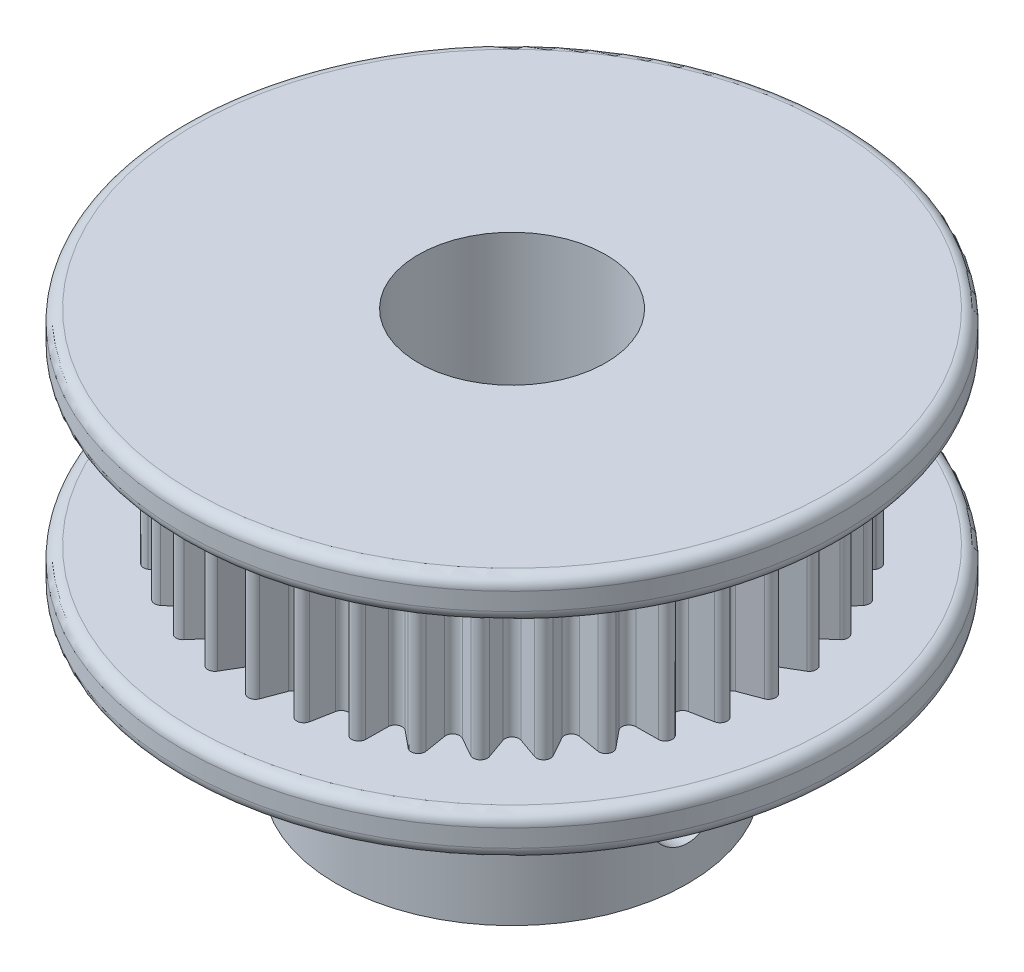
SolidWorks part; units mm, degrees
material "6063-T5"
ref_plane "Front Plane" through (0, 0, 0) normal (0, 0, 1) x (1, 0, 0)
ref_plane "Top Plane" through (0, 0, 0) normal (0, 1, 0) x (1, 0, 0)
ref_plane "Right Plane" through (0, 0, 0) normal (1, 0, 0) x (0, 0, -1)
sketch "Sketch1" plane through (0, 0, 0) normal (0, 1, 0) x (1, 0, 0)
  circle A0 centre (0, 0) radius 7.5
  dimension "D1" = 15
extrude "Boss-Extrude1" add sketch "Sketch1" along normal blind 7 contours A0
sketch "Sketch7" plane through (0, 7, 0) normal (0, 1, 0) x (1, 0, 0)
  circle A0 centre (0, 0) radius 14.065
  dimension "D1" = 28.13
extrude "Boss-Extrude5" add sketch "Sketch7" along normal blind 1.75
sketch "Sketch9" plane through (0, 8.75, 0) normal (0, 1, 0) x (1, 0, 0)
  line L0 (0.2807, 11.056) -> (0.6178, 10.1631)
  line L1 (1.1564, 10.116) -> (1.6435, 10.9367)
  line L2 (0, 10.95) -> (0, 0) construction
  line L3 (1.9014, 10.7836) -> (0, 0) construction
  line L4 (2.1962, 10.8393) -> (2.3732, 9.9015)
  line L5 (0, 10.95) -> (1.9014, 10.7836) construction
  line L6 (0.9507, 10.8668) -> (0, 0)
  line L7 (2.8955, 9.7615) -> (3.5176, 10.4852)
  line L8 (4.0451, 10.2932) -> (4.0565, 9.3389)
  line L9 (4.5466, 9.1104) -> (5.2849, 9.7151)
  line L10 (5.771, 9.4344) -> (5.6166, 8.4926)
  line L11 (6.0595, 8.1825) -> (6.8916, 8.6498)
  line L12 (7.3216, 8.289) -> (7.006, 7.3883)
  line L13 (7.3883, 7.006) -> (8.289, 7.3216)
  line L14 (8.6498, 6.8916) -> (8.1825, 6.0595)
  line L15 (8.4926, 5.6166) -> (9.4344, 5.771)
  line L16 (9.7151, 5.2849) -> (9.1104, 4.5466)
  line L17 (9.3389, 4.0565) -> (10.2932, 4.0451)
  line L18 (10.4852, 3.5176) -> (9.7615, 2.8955)
  line L19 (9.9015, 2.3732) -> (10.8393, 2.1962)
  line L20 (10.9367, 1.6435) -> (10.116, 1.1564)
  line L21 (10.1631, 0.6178) -> (11.056, 0.2807)
  line L22 (11.056, -0.2807) -> (10.1631, -0.6178)
  line L23 (10.116, -1.1564) -> (10.9367, -1.6435)
  line L24 (10.8393, -2.1962) -> (9.9015, -2.3732)
  line L25 (9.7615, -2.8955) -> (10.4852, -3.5176)
  line L26 (10.2932, -4.0451) -> (9.3389, -4.0565)
  line L27 (9.1104, -4.5466) -> (9.7151, -5.2849)
  line L28 (9.4344, -5.771) -> (8.4926, -5.6166)
  line L29 (8.1825, -6.0595) -> (8.6498, -6.8916)
  line L30 (8.289, -7.3216) -> (7.3883, -7.006)
  line L31 (7.006, -7.3883) -> (7.3216, -8.289)
  line L32 (6.8916, -8.6498) -> (6.0595, -8.1825)
  line L33 (5.6166, -8.4926) -> (5.771, -9.4344)
  line L34 (5.2849, -9.7151) -> (4.5466, -9.1104)
  line L35 (4.0565, -9.3389) -> (4.0451, -10.2932)
  line L36 (3.5176, -10.4852) -> (2.8955, -9.7615)
  line L37 (2.3732, -9.9015) -> (2.1962, -10.8393)
  line L38 (1.6435, -10.9367) -> (1.1564, -10.116)
  line L39 (0.6178, -10.1631) -> (0.2807, -11.056)
  line L40 (-0.2807, -11.056) -> (-0.6178, -10.1631)
  line L41 (-1.1564, -10.116) -> (-1.6435, -10.9367)
  line L42 (-2.1962, -10.8393) -> (-2.3732, -9.9015)
  line L43 (-2.8955, -9.7615) -> (-3.5176, -10.4852)
  line L44 (-4.0451, -10.2932) -> (-4.0565, -9.3389)
  line L45 (-4.5466, -9.1104) -> (-5.2849, -9.7151)
  line L46 (-5.771, -9.4344) -> (-5.6166, -8.4926)
  line L47 (-6.0595, -8.1825) -> (-6.8916, -8.6498)
  line L48 (-7.3216, -8.289) -> (-7.006, -7.3883)
  line L49 (-7.3883, -7.006) -> (-8.289, -7.3216)
  line L50 (-8.6498, -6.8916) -> (-8.1825, -6.0595)
  line L51 (-8.4926, -5.6166) -> (-9.4344, -5.771)
  line L52 (-9.7151, -5.2849) -> (-9.1104, -4.5466)
  line L53 (-9.3389, -4.0565) -> (-10.2932, -4.0451)
  line L54 (-10.4852, -3.5176) -> (-9.7615, -2.8955)
  line L55 (-9.9015, -2.3732) -> (-10.8393, -2.1962)
  line L56 (-10.9367, -1.6435) -> (-10.116, -1.1564)
  line L57 (-10.1631, -0.6178) -> (-11.056, -0.2807)
  line L58 (-11.056, 0.2807) -> (-10.1631, 0.6178)
  line L59 (-10.116, 1.1564) -> (-10.9367, 1.6435)
  line L60 (-10.8393, 2.1962) -> (-9.9015, 2.3732)
  line L61 (-9.7615, 2.8955) -> (-10.4852, 3.5176)
  line L62 (-10.2932, 4.0451) -> (-9.3389, 4.0565)
  line L63 (-9.1104, 4.5466) -> (-9.7151, 5.2849)
  line L64 (-9.4344, 5.771) -> (-8.4926, 5.6166)
  line L65 (-8.1825, 6.0595) -> (-8.6498, 6.8916)
  line L66 (-8.289, 7.3216) -> (-7.3883, 7.006)
  line L67 (-7.006, 7.3883) -> (-7.3216, 8.289)
  line L68 (-6.8916, 8.6498) -> (-6.0595, 8.1825)
  line L69 (-5.6166, 8.4926) -> (-5.771, 9.4344)
  line L70 (-5.2849, 9.7151) -> (-4.5466, 9.1104)
  line L71 (-4.0565, 9.3389) -> (-4.0451, 10.2932)
  line L72 (-3.5176, 10.4852) -> (-2.8955, 9.7615)
  line L73 (-2.3732, 9.9015) -> (-2.1962, 10.8393)
  line L74 (-1.6435, 10.9367) -> (-1.1564, 10.116)
  line L75 (-0.6178, 10.1631) -> (-0.2807, 11.056)
  circle A0 centre (0, 0) radius 11.25 construction
  arc A1 (0.2807, 11.056) -> (0, 11.25) centre (0, 10.95) ccw
  arc A2 (2.1962, 10.8393) -> (1.9535, 11.0791) centre (1.9014, 10.7836) ccw
  arc A3 (1.9535, 11.0791) -> (1.6435, 10.9367) centre (1.9014, 10.7836) ccw
  arc A4 (0.6178, 10.1631) -> (1.1564, 10.116) centre (0.8984, 10.2691) ccw
  arc A5 (2.3732, 9.9015) -> (2.8955, 9.7615) centre (2.668, 9.9571) ccw
  arc A6 (3.8477, 10.5715) -> (3.5176, 10.4852) centre (3.7451, 10.2896) ccw
  arc A7 (4.0451, 10.2932) -> (3.8477, 10.5715) centre (3.7451, 10.2896) ccw
  arc A8 (4.0565, 9.3389) -> (4.5466, 9.1104) centre (4.3565, 9.3425) ccw
  arc A9 (5.625, 9.7428) -> (5.2849, 9.7151) centre (5.475, 9.483) ccw
  arc A10 (5.771, 9.4344) -> (5.625, 9.7428) centre (5.475, 9.483) ccw
  arc A11 (5.6166, 8.4926) -> (6.0595, 8.1825) centre (5.9126, 8.4441) ccw
  arc A12 (7.2314, 8.618) -> (6.8916, 8.6498) centre (7.0385, 8.3882) ccw
  arc A13 (7.3216, 8.289) -> (7.2314, 8.618) centre (7.0385, 8.3882) ccw
  arc A14 (7.006, 7.3883) -> (7.3883, 7.006) centre (7.2891, 7.2891) ccw
  arc A15 (8.618, 7.2314) -> (8.289, 7.3216) centre (8.3882, 7.0385) ccw
  arc A16 (8.6498, 6.8916) -> (8.618, 7.2314) centre (8.3882, 7.0385) ccw
  arc A17 (8.1825, 6.0595) -> (8.4926, 5.6166) centre (8.4441, 5.9126) ccw
  arc A18 (9.7428, 5.625) -> (9.4344, 5.771) centre (9.483, 5.475) ccw
  arc A19 (9.7151, 5.2849) -> (9.7428, 5.625) centre (9.483, 5.475) ccw
  arc A20 (9.1104, 4.5466) -> (9.3389, 4.0565) centre (9.3425, 4.3565) ccw
  arc A21 (10.5715, 3.8477) -> (10.2932, 4.0451) centre (10.2896, 3.7451) ccw
  arc A22 (10.4852, 3.5176) -> (10.5715, 3.8477) centre (10.2896, 3.7451) ccw
  arc A23 (9.7615, 2.8955) -> (9.9015, 2.3732) centre (9.9571, 2.668) ccw
  arc A24 (11.0791, 1.9535) -> (10.8393, 2.1962) centre (10.7836, 1.9014) ccw
  arc A25 (10.9367, 1.6435) -> (11.0791, 1.9535) centre (10.7836, 1.9014) ccw
  arc A26 (10.116, 1.1564) -> (10.1631, 0.6178) centre (10.2691, 0.8984) ccw
  arc A27 (11.25, 0) -> (11.056, 0.2807) centre (10.95, 0) ccw
  arc A28 (11.056, -0.2807) -> (11.25, 0) centre (10.95, 0) ccw
  arc A29 (10.1631, -0.6178) -> (10.116, -1.1564) centre (10.2691, -0.8984) ccw
  arc A30 (11.0791, -1.9535) -> (10.9367, -1.6435) centre (10.7836, -1.9014) ccw
  arc A31 (10.8393, -2.1962) -> (11.0791, -1.9535) centre (10.7836, -1.9014) ccw
  arc A32 (9.9015, -2.3732) -> (9.7615, -2.8955) centre (9.9571, -2.668) ccw
  arc A33 (10.5715, -3.8477) -> (10.4852, -3.5176) centre (10.2896, -3.7451) ccw
  arc A34 (10.2932, -4.0451) -> (10.5715, -3.8477) centre (10.2896, -3.7451) ccw
  arc A35 (9.3389, -4.0565) -> (9.1104, -4.5466) centre (9.3425, -4.3565) ccw
  arc A36 (9.7428, -5.625) -> (9.7151, -5.2849) centre (9.483, -5.475) ccw
  arc A37 (9.4344, -5.771) -> (9.7428, -5.625) centre (9.483, -5.475) ccw
  arc A38 (8.4926, -5.6166) -> (8.1825, -6.0595) centre (8.4441, -5.9126) ccw
  arc A39 (8.618, -7.2314) -> (8.6498, -6.8916) centre (8.3882, -7.0385) ccw
  arc A40 (8.289, -7.3216) -> (8.618, -7.2314) centre (8.3882, -7.0385) ccw
  arc A41 (7.3883, -7.006) -> (7.006, -7.3883) centre (7.2891, -7.2891) ccw
  arc A42 (7.2314, -8.618) -> (7.3216, -8.289) centre (7.0385, -8.3882) ccw
  arc A43 (6.8916, -8.6498) -> (7.2314, -8.618) centre (7.0385, -8.3882) ccw
  arc A44 (6.0595, -8.1825) -> (5.6166, -8.4926) centre (5.9126, -8.4441) ccw
  arc A45 (5.625, -9.7428) -> (5.771, -9.4344) centre (5.475, -9.483) ccw
  arc A46 (5.2849, -9.7151) -> (5.625, -9.7428) centre (5.475, -9.483) ccw
  arc A47 (4.5466, -9.1104) -> (4.0565, -9.3389) centre (4.3565, -9.3425) ccw
  arc A48 (3.8477, -10.5715) -> (4.0451, -10.2932) centre (3.7451, -10.2896) ccw
  arc A49 (3.5176, -10.4852) -> (3.8477, -10.5715) centre (3.7451, -10.2896) ccw
  arc A50 (2.8955, -9.7615) -> (2.3732, -9.9015) centre (2.668, -9.9571) ccw
  arc A51 (1.9535, -11.0791) -> (2.1962, -10.8393) centre (1.9014, -10.7836) ccw
  arc A52 (1.6435, -10.9367) -> (1.9535, -11.0791) centre (1.9014, -10.7836) ccw
  arc A53 (1.1564, -10.116) -> (0.6178, -10.1631) centre (0.8984, -10.2691) ccw
  arc A54 (0, -11.25) -> (0.2807, -11.056) centre (0, -10.95) ccw
  arc A55 (-0.2807, -11.056) -> (0, -11.25) centre (0, -10.95) ccw
  arc A56 (-0.6178, -10.1631) -> (-1.1564, -10.116) centre (-0.8984, -10.2691) ccw
  arc A57 (-1.9535, -11.0791) -> (-1.6435, -10.9367) centre (-1.9014, -10.7836) ccw
  arc A58 (-2.1962, -10.8393) -> (-1.9535, -11.0791) centre (-1.9014, -10.7836) ccw
  arc A59 (-2.3732, -9.9015) -> (-2.8955, -9.7615) centre (-2.668, -9.9571) ccw
  arc A60 (-3.8477, -10.5715) -> (-3.5176, -10.4852) centre (-3.7451, -10.2896) ccw
  arc A61 (-4.0451, -10.2932) -> (-3.8477, -10.5715) centre (-3.7451, -10.2896) ccw
  arc A62 (-4.0565, -9.3389) -> (-4.5466, -9.1104) centre (-4.3565, -9.3425) ccw
  arc A63 (-5.625, -9.7428) -> (-5.2849, -9.7151) centre (-5.475, -9.483) ccw
  arc A64 (-5.771, -9.4344) -> (-5.625, -9.7428) centre (-5.475, -9.483) ccw
  arc A65 (-5.6166, -8.4926) -> (-6.0595, -8.1825) centre (-5.9126, -8.4441) ccw
  arc A66 (-7.2314, -8.618) -> (-6.8916, -8.6498) centre (-7.0385, -8.3882) ccw
  arc A67 (-7.3216, -8.289) -> (-7.2314, -8.618) centre (-7.0385, -8.3882) ccw
  arc A68 (-7.006, -7.3883) -> (-7.3883, -7.006) centre (-7.2891, -7.2891) ccw
  arc A69 (-8.618, -7.2314) -> (-8.289, -7.3216) centre (-8.3882, -7.0385) ccw
  arc A70 (-8.6498, -6.8916) -> (-8.618, -7.2314) centre (-8.3882, -7.0385) ccw
  arc A71 (-8.1825, -6.0595) -> (-8.4926, -5.6166) centre (-8.4441, -5.9126) ccw
  arc A72 (-9.7428, -5.625) -> (-9.4344, -5.771) centre (-9.483, -5.475) ccw
  arc A73 (-9.7151, -5.2849) -> (-9.7428, -5.625) centre (-9.483, -5.475) ccw
  arc A74 (-9.1104, -4.5466) -> (-9.3389, -4.0565) centre (-9.3425, -4.3565) ccw
  arc A75 (-10.5715, -3.8477) -> (-10.2932, -4.0451) centre (-10.2896, -3.7451) ccw
  arc A76 (-10.4852, -3.5176) -> (-10.5715, -3.8477) centre (-10.2896, -3.7451) ccw
  arc A77 (-9.7615, -2.8955) -> (-9.9015, -2.3732) centre (-9.9571, -2.668) ccw
  arc A78 (-11.0791, -1.9535) -> (-10.8393, -2.1962) centre (-10.7836, -1.9014) ccw
  arc A79 (-10.9367, -1.6435) -> (-11.0791, -1.9535) centre (-10.7836, -1.9014) ccw
  arc A80 (-10.116, -1.1564) -> (-10.1631, -0.6178) centre (-10.2691, -0.8984) ccw
  arc A81 (-11.25, 0) -> (-11.056, -0.2807) centre (-10.95, 0) ccw
  arc A82 (-11.056, 0.2807) -> (-11.25, 0) centre (-10.95, 0) ccw
  arc A83 (-10.1631, 0.6178) -> (-10.116, 1.1564) centre (-10.2691, 0.8984) ccw
  arc A84 (-11.0791, 1.9535) -> (-10.9367, 1.6435) centre (-10.7836, 1.9014) ccw
  arc A85 (-10.8393, 2.1962) -> (-11.0791, 1.9535) centre (-10.7836, 1.9014) ccw
  arc A86 (-9.9015, 2.3732) -> (-9.7615, 2.8955) centre (-9.9571, 2.668) ccw
  arc A87 (-10.5715, 3.8477) -> (-10.4852, 3.5176) centre (-10.2896, 3.7451) ccw
  arc A88 (-10.2932, 4.0451) -> (-10.5715, 3.8477) centre (-10.2896, 3.7451) ccw
  arc A89 (-9.3389, 4.0565) -> (-9.1104, 4.5466) centre (-9.3425, 4.3565) ccw
  arc A90 (-9.7428, 5.625) -> (-9.7151, 5.2849) centre (-9.483, 5.475) ccw
  arc A91 (-9.4344, 5.771) -> (-9.7428, 5.625) centre (-9.483, 5.475) ccw
  arc A92 (-8.4926, 5.6166) -> (-8.1825, 6.0595) centre (-8.4441, 5.9126) ccw
  arc A93 (-8.618, 7.2314) -> (-8.6498, 6.8916) centre (-8.3882, 7.0385) ccw
  arc A94 (-8.289, 7.3216) -> (-8.618, 7.2314) centre (-8.3882, 7.0385) ccw
  arc A95 (-7.3883, 7.006) -> (-7.006, 7.3883) centre (-7.2891, 7.2891) ccw
  arc A96 (-7.2314, 8.618) -> (-7.3216, 8.289) centre (-7.0385, 8.3882) ccw
  arc A97 (-6.8916, 8.6498) -> (-7.2314, 8.618) centre (-7.0385, 8.3882) ccw
  arc A98 (-6.0595, 8.1825) -> (-5.6166, 8.4926) centre (-5.9126, 8.4441) ccw
  arc A99 (-5.625, 9.7428) -> (-5.771, 9.4344) centre (-5.475, 9.483) ccw
  arc A100 (-5.2849, 9.7151) -> (-5.625, 9.7428) centre (-5.475, 9.483) ccw
  arc A101 (-4.5466, 9.1104) -> (-4.0565, 9.3389) centre (-4.3565, 9.3425) ccw
  arc A102 (-3.8477, 10.5715) -> (-4.0451, 10.2932) centre (-3.7451, 10.2896) ccw
  arc A103 (-3.5176, 10.4852) -> (-3.8477, 10.5715) centre (-3.7451, 10.2896) ccw
  arc A104 (-2.8955, 9.7615) -> (-2.3732, 9.9015) centre (-2.668, 9.9571) ccw
  arc A105 (-1.9535, 11.0791) -> (-2.1962, 10.8393) centre (-1.9014, 10.7836) ccw
  arc A106 (-1.6435, 10.9367) -> (-1.9535, 11.0791) centre (-1.9014, 10.7836) ccw
  arc A107 (-1.1564, 10.116) -> (-0.6178, 10.1631) centre (-0.8984, 10.2691) ccw
  arc A108 (0, 11.25) -> (-0.2807, 11.056) centre (0, 10.95) ccw
  point P9 (0, 0)
  point P10 (0, 0)
  point P11 (0, 0)
  point P14 (0.4028, 0.0101)
  point P17 (-0.0772, 0.004)
  point P20 (0, 0)
  point P337 (0, 0)
  dimension "D1" = 0.6
  dimension "D6" = 10
  dimension "D7" = 22.5
  dimension "D2" = 0.6
extrude "Boss-Extrude7" add sketch "Sketch9" along normal blind 7 contours A1 A108 L75 A107 L74 A106 A105 L73 A104 L72 A103 A102 L71 A101 L70 A100 A99 L69 A98 L68 A97 A96 L67 A95 L66 A94 A93 L65 A92 L64 A91 A90 L63 A89 L62 A88 A87 L61 A86 L60 A85 A84 L59 A83 L58 A82 A81 L57 A80 L56 A79
sketch "Sketch8" plane through (0, 15.75, 0) normal (0, 1, 0) x (1, 0, 0)
  circle A1 centre (0, 0) radius 14.065 construction
  circle A2 centre (0, 0) radius 14.065
extrude "Boss-Extrude6" add sketch "Sketch8" along normal blind 1.75
sketch "Sketch4" plane through (0, 0, 0) normal (0, -1, 0) x (1, 0, 0)
  circle A0 centre (0, 0) radius 4
  dimension "D1" = 8
extrude "Cut-Extrude4" cut sketch "Sketch4" against normal through all contours A0
sketch "Sketch5" plane through (0, 0, 0) normal (1, 0, 0) x (0, 0, -1)
  circle A0 centre (0, 3) radius 1.5
  dimension "D1" = 3
  dimension "D2" = 3
extrude "Cut-Extrude2" cut sketch "Sketch5" along normal through all
sketch "Sketch6" plane through (0, 0, 0) normal (0, 0, 1) x (1, 0, 0)
  circle A0 centre (0, 3) radius 1.5
  dimension "D1" = 3
  dimension "D2" = 3
extrude "Cut-Extrude3" cut sketch "Sketch6" against normal through all
ref_plane "Plane1" through (0, 12.25, 0) normal (0, 1, 0) x (1, 0, 0)
fillet "Fillet1" radius 0.5 4 edges at (0, 7, 14.065) (0, 8.75, 14.065) (0, 15.75, 14.065) (0, 17.5, 14.065)
sketch "Sketch10" plane through (0, 15.75, 0) normal (0, -1, 0) x (1, 0, 0)
  circle A0 centre (0, 0) radius 11.25 construction
